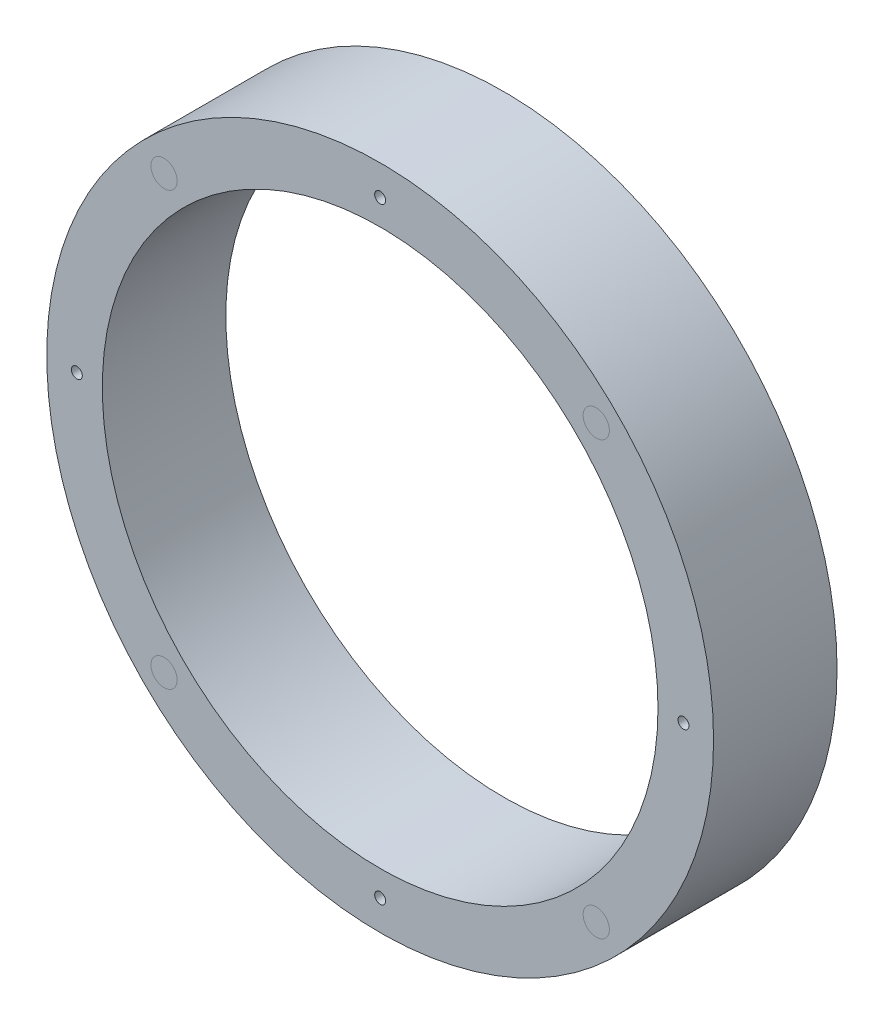
SolidWorks part; units mm, degrees
ref_plane "Front Plane" through (0, 0, 0) normal (0, 0, 1) x (1, 0, 0)
ref_plane "Top Plane" through (0, 0, 0) normal (0, 1, 0) x (1, 0, 0)
ref_plane "Right Plane" through (0, 0, 0) normal (1, 0, 0) x (0, 0, -1)
sketch "Sketch1" plane through (0, 0, 0) normal (0, 0, 1) x (1, 0, 0)
  line L0 (0, 70.5725) -> (0, 76.2) construction
  line L3 (-1.25, 69.3225) -> (12.2983, 69.3225) construction
  circle A0 centre (0, 0) radius 63.5
  circle A1 centre (0, 0) radius 76.2
  circle A2 centre (0, 69.3225) radius 1.25
  circle A3 centre (69.3225, 0) radius 1.25
  circle A4 centre (0, -69.3225) radius 1.25
  circle A5 centre (-69.3225, 0) radius 1.25
  point P19 (0, 0)
  dimension "D1" = 127
  dimension "D2" = 152.4
  dimension "D3" = 2.5
  dimension "D5" = 5.6275
  dimension "D4" = 4
extrude "Boss-Extrude1" add sketch "Sketch1" along normal blind 28.225
sketch "Sketch2" plane through (0, 0, 0) normal (0, 0, -1) x (-1, 0, 0)
  circle A0 centre (0, 69.3225) radius 2.5
  circle A1 centre (69.3225, 0) radius 2.5
  circle A2 centre (0, -69.3225) radius 2.5
  circle A3 centre (-69.3225, 0) radius 2.5
  circle A4 centre (69.3225, 0) radius 1.25 construction
  circle A5 centre (0, -69.3225) radius 1.25 construction
  point P12 (0, 0)
  dimension "D1" = 5
  dimension "D2" = 4
extrude "Cut-Extrude1" cut sketch "Sketch2" against normal blind 6.725
sketch "Sketch3" plane through (0, 0, 28.225) normal (0, 0, 1) x (1, 0, 0)
  line L0 (0, 69.3225) -> (0, 0) construction
  line L1 (0, 0) -> (-79.0122, 79.0122) construction
  line L2 (-53.8815, 53.8815) -> (-53.8815, 44.9013) construction
  line L3 (-53.8815, 44.9013) -> (-44.9013, 44.9013) construction
  line L4 (-53.8815, 44.9013) -> (-46.9345, 51.8484) construction
  circle A0 centre (0, 0) radius 76.2 construction
  circle A1 centre (0, 0) radius 63.5 construction
  circle A2 centre (-49.3914, 49.3914) radius 3
  circle A3 centre (49.3914, 49.3914) radius 3
  circle A4 centre (49.3914, -49.3914) radius 3
  circle A5 centre (-49.3914, -49.3914) radius 3
  point P25 (0, 0)
  dimension "D2" = 6
  dimension "D1" = 45
  dimension "D3" = 4
extrude "Cut-Extrude2" cut sketch "Sketch3" against normal through all
sketch "Sketch4" plane through (0, 0, 28.225) normal (0, 0, 1) x (1, 0, 0)
  circle A0 centre (-49.3914, -49.3914) radius 3 construction
  circle A1 centre (49.3914, -49.3914) radius 3 construction
  circle A2 centre (49.3914, 49.3914) radius 3 construction
  circle A3 centre (-49.3914, 49.3914) radius 3 construction
  circle A4 centre (-49.3914, -49.3914) radius 3
  circle A5 centre (49.3914, -49.3914) radius 3
  circle A6 centre (49.3914, 49.3914) radius 3
  circle A7 centre (-49.3914, 49.3914) radius 3
extrude "Boss-Extrude2" add sketch "Sketch4" against normal blind 6.45 separate body
